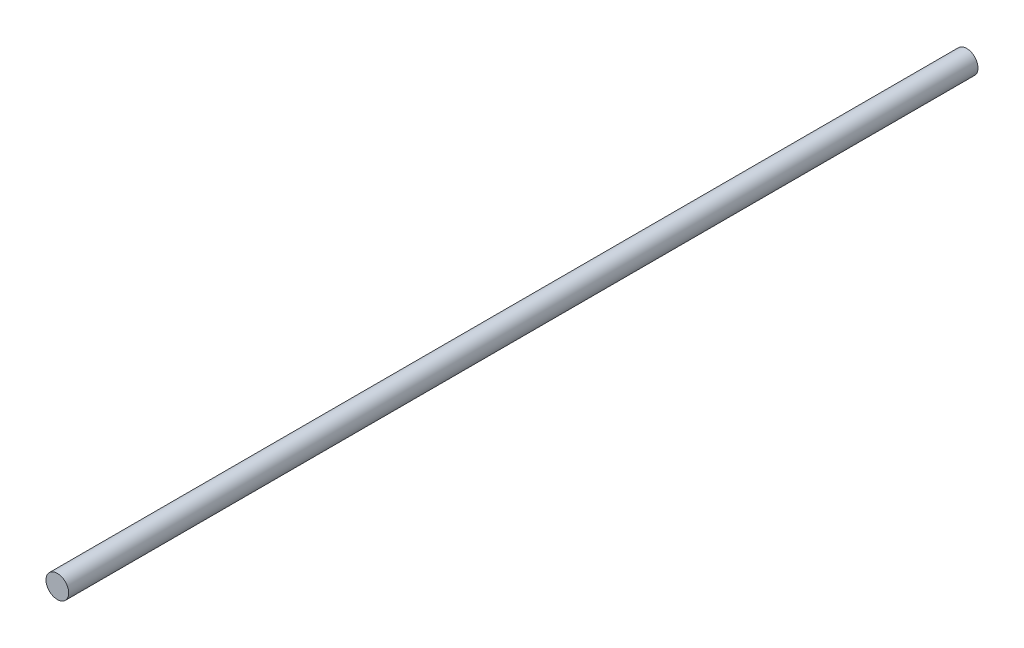
SolidWorks part; units mm, degrees
material "ABS"
ref_plane "Plano frontal" through (0, 0, 0) normal (0, 0, 1) x (1, 0, 0)
ref_plane "Plano superior" through (0, 0, 0) normal (0, 1, 0) x (1, 0, 0)
ref_plane "Plano direito" through (0, 0, 0) normal (1, 0, 0) x (0, 0, -1)
sketch "Sketch1" plane through (0, 0, 0) normal (0, 0, 1) x (1, 0, 0)
  circle A0 centre (0, 0) radius 0.875
extrude "Extrude1" add sketch "Sketch1" along normal blind 70
